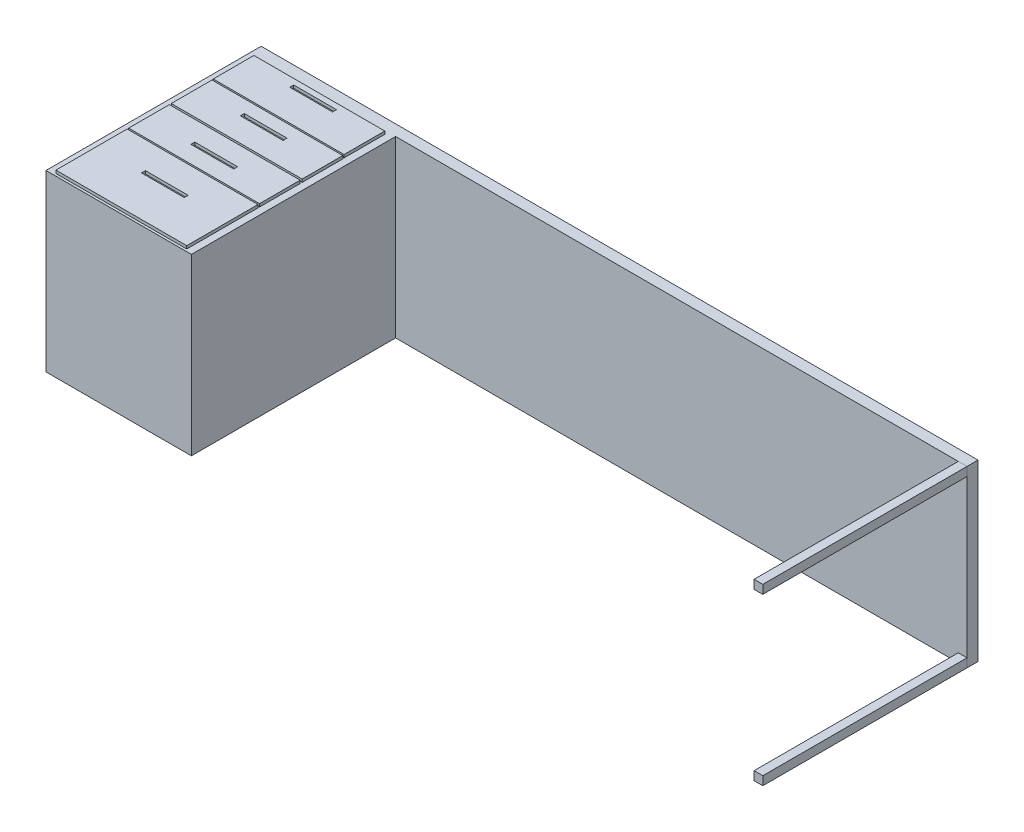
SolidWorks part; units mm, degrees
ref_plane "Front Plane" through (0, 0, 0) normal (0, 0, 1) x (1, 0, 0)
ref_plane "Top Plane" through (0, 0, 0) normal (0, 1, 0) x (1, 0, 0)
ref_plane "Right Plane" through (0, 0, 0) normal (1, 0, 0) x (0, 0, -1)
sketch "Sketch1" plane through (0, 0, 0) normal (0, 1, 0) x (1, 0, 0)
  line L0 (-0.9485, 0) -> (-0.9485, 740)
  line L1 (-0.9485, 740) -> (2464.0515, 740)
  line L2 (2464.0515, 740) -> (2464.0515, 702.2632)
  line L3 (1965, 702.2632) -> (2464.0515, 702.2632)
  line L5 (1965, 702.2632) -> (499.0515, 702.2632)
  line L6 (499.0515, 702.2632) -> (499.0515, 0)
  line L7 (499.0515, 0) -> (-0.9485, 0)
  dimension "D2" = 740
  dimension "D3" = 2465
  dimension "D5" = 500
extrude "Boss-Extrude1" add sketch "Sketch1" along normal blind 600 contours L1 L2 L3 L5 L6 L7 L0
sketch "Sketch2" plane through (0, 600, 0) normal (0, 1, 0) x (1, 0, 0)
  line L0 (499.0515, 702.2632) -> (499.0515, 0) construction
  line L1 (24.0528, 690) -> (474.0528, 690)
  line L2 (24.0528, 690) -> (24.0528, 550)
  line L3 (24.0528, 550) -> (474.0528, 550)
  line L4 (474.0528, 690) -> (474.0528, 550)
  line L5 (25.0013, 544.7895) -> (475.0013, 544.7895)
  line L6 (25.0013, 544.7895) -> (25.0013, 404.7895)
  line L7 (25.0013, 404.7895) -> (475.0013, 404.7895)
  line L8 (475.0013, 544.7895) -> (475.0013, 404.7895)
  line L9 (25.0013, 398.2469) -> (475.0013, 398.2469)
  line L10 (25.0013, 398.2469) -> (25.0013, 258.2469)
  line L11 (25.0013, 258.2469) -> (475.0013, 258.2469)
  line L12 (475.0013, 398.2469) -> (475.0013, 258.2469)
  line L13 (25.0013, 253.0365) -> (475.0013, 253.0365)
  line L14 (-0.9485, 740) -> (2464.0515, 740) construction
  line L15 (25.0013, 253.0365) -> (25.0013, 8.0365)
  line L16 (25.0013, 8.0365) -> (475.0013, 8.0365)
  line L17 (475.0013, 253.0365) -> (475.0013, 8.0365)
  line L18 (180.4489, 486.8982) -> (327.3623, 486.8982)
  line L27 (180.4489, 670.4799) -> (327.3623, 670.4799)
  line L28 (180.4489, 670.4799) -> (180.4489, 656.8982)
  line L29 (180.4489, 656.8982) -> (327.3623, 656.8982)
  line L30 (327.3623, 670.4799) -> (327.3623, 656.8982)
  line L31 (180.4489, 500.4799) -> (327.3623, 500.4799)
  line L32 (180.4489, 500.4799) -> (180.4489, 486.8982)
  line L33 (327.3623, 500.4799) -> (327.3623, 486.8982)
  line L34 (180.4489, 316.8982) -> (327.3623, 316.8982)
  line L35 (180.4489, 330.4799) -> (327.3623, 330.4799)
  line L36 (180.4489, 330.4799) -> (180.4489, 316.8982)
  line L37 (327.3623, 330.4799) -> (327.3623, 316.8982)
  line L38 (180.4489, 146.8982) -> (327.3623, 146.8982)
  line L39 (180.4489, 160.4799) -> (327.3623, 160.4799)
  line L40 (180.4489, 160.4799) -> (180.4489, 146.8982)
  line L41 (327.3623, 160.4799) -> (327.3623, 146.8982)
  dimension "D1" = 140
  dimension "D2" = 450
  dimension "D3" = 24.9987
  dimension "D4" = 5.2105
  dimension "D5" = 50
  dimension "D6" = 245
extrude "Boss-Extrude2" add sketch "Sketch2" along normal blind 10
sketch "Sketch3" plane through (0, 0, -702.2632) normal (0, 0, 1) x (1, 0, 0)
  line L0 (2464.0515, 30) -> (2434.0515, 30)
  line L1 (2464.0515, 600) -> (2434.0515, 600)
  line L2 (2464.0515, 600) -> (2464.0515, 570)
  line L3 (2464.0515, 570) -> (2434.0515, 570)
  line L4 (2434.0515, 600) -> (2434.0515, 570)
  line L5 (2464.0515, 30) -> (2464.0515, 0)
  line L6 (2464.0515, 0) -> (2434.0515, 0)
  line L7 (2434.0515, 30) -> (2434.0515, 0)
  dimension "D1" = 30
  dimension "D2" = 30
  dimension "D3" = 30
  dimension "D4" = 30
extrude "Boss-Extrude3" add sketch "Sketch3" along normal up to surface (702.2632 mm away) separate body up to face at (249.0515, 300, 0)
